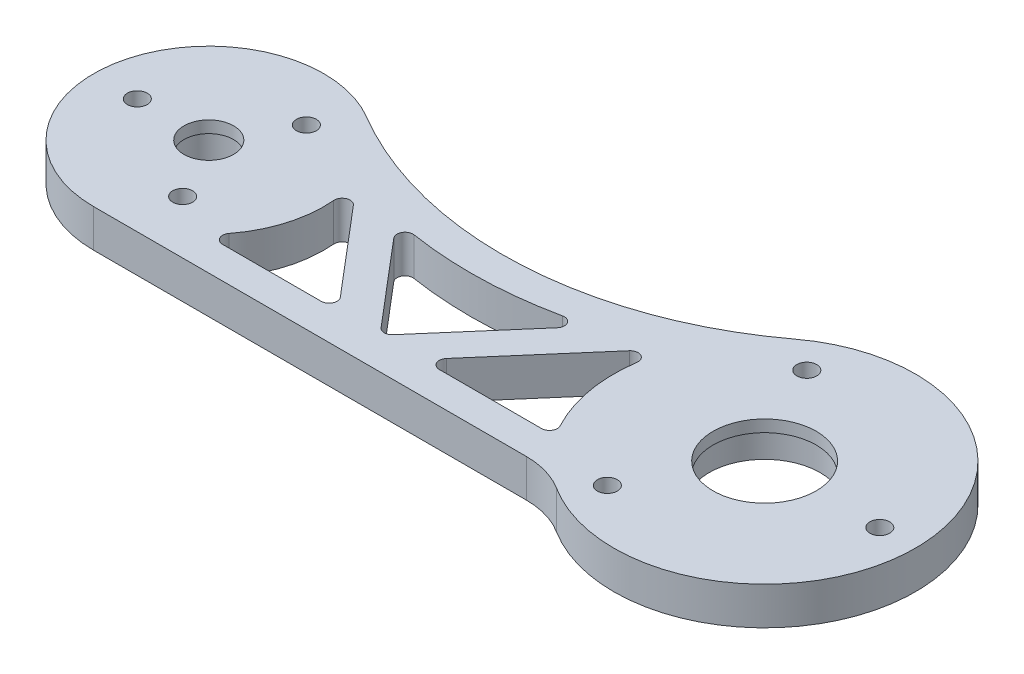
SolidWorks part; units mm, degrees
material "Stainless Steel (ferritic)"
ref_plane "Front Plane" through (0, 0, 0) normal (0, 0, 1) x (1, 0, 0)
ref_plane "Top Plane" through (0, 0, 0) normal (0, 1, 0) x (1, 0, 0)
ref_plane "Right Plane" through (0, 0, 0) normal (1, 0, 0) x (0, 0, -1)
sketch "Sketch1" plane through (0, 0, 0) normal (0, 1, 0) x (1, 0, 0)
  line L0 (-35, 0) -> (35, 0) construction
  line L1 (-35, 14.5) -> (19.4839, 14.5)
  line L2 (-35, -14.5) -> (19.4839, -14.5)
  arc A0 (-35, 14.5) -> (-35, -14.5) centre (-35, 0) ccw
  arc A1 (24.8343, -16.0517) -> (24.8343, 16.0517) centre (35, 0) ccw
  arc A2 (19.4839, 14.5) -> (24.8343, 16.0517) centre (19.4839, 24.5) ccw
  arc A3 (24.8343, -16.0517) -> (19.4839, -14.5) centre (19.4839, -24.5) ccw
  dimension "D1" = 29
  dimension "D2" = 38
  dimension "D4" = 20
  dimension "D3" = 70
extrude "Boss-Extrude1" add sketch "Sketch1" along normal blind 4.7625
sketch "Sketch2" plane through (0, 4.7625, 0) normal (0, 1, 0) x (1, 0, 0)
  line L0 (-14.4545, 6) -> (6.022, 6) construction
  line L1 (-35, 14.5) -> (27.6098, 17.5039)
  arc A0 (-27.5958, 12.4671) -> (23.6098, 15.2074) centre (-4.042, 52.1262) ccw
  arc A1 (-27.5958, 12.4671) -> (-24.743, 10.2491) centre (-35, 0) ccw construction
  circle A2 centre (35, 0) radius 19 construction
  arc A3 (24.8343, -16.0517) -> (24.8343, 16.0517) centre (35, 0) ccw construction
  arc A4 (-35, 14.5) -> (-27.5958, 12.4671) centre (-35, 0) cw
  arc A5 (23.6098, 15.2074) -> (27.6098, 17.5039) centre (35, 0) cw
  dimension "D1" = 6
  dimension "D2" = 4
extrude "Cut-Extrude1" cut sketch "Sketch2" against normal through all
sketch "Sketch3" plane through (0, 4.7625, 0) normal (0, 1, 0) x (1, 0, 0)
  line L0 (-25, -10.5) -> (-8.1831, -10.5)
  line L1 (-35, -14.5) -> (19.4839, -14.5) construction
  line L2 (-8.1831, -10.5) -> (-21.4314, 5.1129)
  line L3 (-14.4755, 3.0978) -> (-2.9371, -10.5)
  line L4 (-2.9371, -10.5) -> (9.4563, 3.8517)
  line L5 (17.2357, 6.7401) -> (2.348, -10.5)
  line L6 (-12.9584, 1.31) -> (-16.0083, -1.278) construction
  line L7 (6.5385, 0.4729) -> (9.566, -2.1415) construction
  line L8 (2.348, -10.5) -> (19.1649, -10.5)
  arc A0 (-25, -10.5) -> (-21.4314, 5.1129) centre (-35, 0) ccw
  arc A1 (17.2357, 6.7401) -> (19.1649, -10.5) centre (35, 0) ccw
  arc A2 (24.8343, -16.0517) -> (23.6098, 15.2074) centre (35, 0) ccw construction
  arc A3 (-27.5958, 12.4671) -> (-35, -14.5) centre (-35, 0) ccw construction
  arc A6 (-29.6383, 9.0279) -> (26.0078, 12.0058) centre (-4.042, 52.1262) ccw
  arc A7 (-14.4755, 3.0978) -> (9.4563, 3.8517) centre (-4.042, 52.1262) ccw
  dimension "D2" = 4
  dimension "D3" = 4
  dimension "D1" = 4
extrude "Cut-Extrude2" cut sketch "Sketch3" against normal through all
fillet "Fillet1" radius 1 9 edges at (19.1649, 2.3813, 10.5) (2.348, 2.3813, 10.5) (17.2357, 2.3813, -6.7401) (9.4563, 2.3813, -3.8517) (-2.9371, 2.3813, 10.5) (-8.1831, 2.3813, 10.5) (-14.4755, 2.3813, -3.0978) (-21.4314, 2.3813, -5.1129) (-25, 2.3813, 10.5)
mirror "Mirror1" [suppressed] about plane through (0, 0, 0) normal (0, 0, 1)
sketch "Sketch4" plane through (0, 4.7625, 0) normal (0, 1, 0) x (1, 0, 0)
  circle A0 centre (-35, 0) radius 4
  dimension "D1" = 8
extrude "Boss-Extrude3" add sketch "Sketch4" against normal through all
sketch "Sketch5" plane through (0, 4.7625, 0) normal (0, 1, 0) x (1, 0, 0)
  circle A0 centre (-35, 0) radius 3.125
  dimension "D1" = 6.25
extrude "Cut-Extrude3" cut sketch "Sketch5" against normal through all
sketch "Sketch6" plane through (0, 0, 0) normal (0, 1, 0) x (1, 0, 0)
  circle A0 centre (-35, 0) radius 3.5
  dimension "D1" = 7
extrude "Cut-Extrude4" cut sketch "Sketch6" along normal offset from surface (3.2625 mm away) 1.5 up to face at (-35, 4.7625, 3.125)
sketch "Sketch7" plane through (0, 0, 0) normal (0, -1, 0) x (1, 0, 0)
  circle A0 centre (35, 0) radius 6.5
  dimension "D1" = 13
extrude "Cut-Extrude5" cut sketch "Sketch7" against normal through all
sketch "Sketch8" plane through (0, 0, 0) normal (0, -1, 0) x (1, 0, 0)
  circle A0 centre (35, 0) radius 7
  dimension "D1" = 14
extrude "Cut-Extrude6" cut sketch "Sketch8" against normal offset from surface (3.2625 mm away) 1.5 up to face at (35, 4.7625, -6.5)
sketch "Sketch9" plane through (0, 0, 0) normal (0, -1, 0) x (1, 0, 0)
  circle A0 centre (35, 0) radius 5
  arc A1 (23.6098, -15.2074) -> (24.8343, 16.0517) centre (35, 0) ccw construction
  dimension "D1" = 10
extrude "Cut-Extrude7" [suppressed] cut sketch "Sketch9" against normal through all
sketch "Sketch10" [suppressed] plane through (0, 0, 0) normal (0, -1, 0) x (1, 0, 0)
  circle A0 centre (35, 0) radius 7.5
  circle A1 centre (35, 0) radius 5 construction
  dimension "D1" = 2.5
extrude "Cut-Extrude8" [suppressed] cut sketch "Sketch10" against normal blind 2
sketch "Sketch11" plane through (0, 4.7625, 0) normal (0, 1, 0) x (1, 0, 0)
  circle A0 centre (-35, 0) radius 3.5
  dimension "D1" = 7
extrude "Cut-Extrude9" [suppressed] cut sketch "Sketch11" against normal offset from surface (3.2625 mm away) 1.5
sketch "Sketch12" [suppressed] plane through (0, 1.5, 0) normal (0, 1, 0) x (1, 0, 0)
  circle A0 centre (-35, 0) radius 3
  circle A1 centre (-35, 0) radius 3.5 construction
  dimension "D1" = 0.5
extrude "Cut-Extrude10" [suppressed] cut sketch "Sketch12" against normal through all
hole_wizard "M3x0.5 Tapped Hole1" positions "Sketch14" profile "Sketch13" tap size "M3x0.5" standard "Ansi Metric" end condition through all
sketch "Sketch14" plane through (0, 0, 0) normal (0, -1, 0) x (1, 0, 0)
  line L0 (-44, 0) -> (-35, 0) construction
  line L1 (-35, 0) -> (-30.5, 7.7942) construction
  line L4 (-35, 0) -> (-30.5, -7.7942) construction
  line L7 (49.5, 0) -> (35, 0) construction
  line L8 (35, 0) -> (27.75, 12.5574) construction
  line L11 (35, 0) -> (27.75, -12.5574) construction
  circle A0 centre (-35, 0) radius 9 construction
  circle A1 centre (35, 0) radius 14.5 construction
  point P0 (27.75, -12.5574)
  point P1 (27.75, 12.5574)
  point P3 (49.5, 0)
  point P5 (-44, 0)
  point P7 (-30.5, 7.7942)
  point P9 (-30.5, -7.7942)
  dimension "D1" = 18
  dimension "D2" = 29
  dimension "D3" = 120
  dimension "D4" = 120
  dimension "D5" = 120
  dimension "D6" = 120
sketch "Sketch13" plane through (27.75, 0, -12.5574) normal (1, 0, 0) x (0, 0, -1)
  line L0 (0, 0) -> (0, 4.7625)
  line L1 (0, 4.7625) -> (1.25, 4.7625)
  line L2 (1.25, 4.7625) -> (1.25, 0)
  line L5 (1.25, 0) -> (0, 0)
  line L11 (0, -6.35) -> (0, 107.95) construction
  dimension "Thru Tap Drill Dia." = 2.5
  dimension "Thru Tap Drill Depth" = 4.7625
cosmetic thread "Hole Thread1" parameters "D2"=3
cosmetic thread "Hole Thread2" parameters "D2"=3
cosmetic thread "Hole Thread3" parameters "D2"=3
cosmetic thread "Hole Thread4" parameters "D2"=3
cosmetic thread "Hole Thread5" parameters "D2"=3
cosmetic thread "Hole Thread6" parameters "D2"=3
hole_wizard "M3x0.5 Tapped Hole2" positions "Sketch16" profile "Sketch15" tap size "M3x0.5" standard "Ansi Metric"
sketch "Sketch16" plane through (0, 4.7625, 0) normal (0, 1, 0) x (-1, 0, 0)
  line L0 (44, 0) -> (35, 0) construction
  line L1 (35, 0) -> (30.5, 7.7942) construction
  line L4 (35, 0) -> (30.5, -7.7942) construction
  circle A0 centre (35, 0) radius 9 construction
  point P0 (30.5, 7.7942)
  point P1 (44, 0)
  point P3 (30.5, -7.7942)
  dimension "D1" = 18
  dimension "D2" = 120
  dimension "D3" = 120
sketch "Sketch15" plane through (-30.5, 4.7625, 7.7942) normal (1, 0, 0) x (0, 0, 1)
  line L0 (0, 0) -> (0, 4.7625)
  line L1 (0, 4.7625) -> (1.25, 4.7625)
  line L2 (1.25, 4.7625) -> (1.25, 0)
  line L5 (1.25, 0) -> (0, 0)
  line L11 (0, -6.35) -> (0, 107.95) construction
  dimension "Thru Tap Drill Dia." = 2.5
  dimension "Thru Tap Drill Depth" = 4.7625
cosmetic thread "Hole Thread7" [suppressed] parameters "D2"=3
cosmetic thread "Hole Thread8" [suppressed] parameters "D2"=3
cosmetic thread "Hole Thread9" [suppressed] parameters "D2"=3
